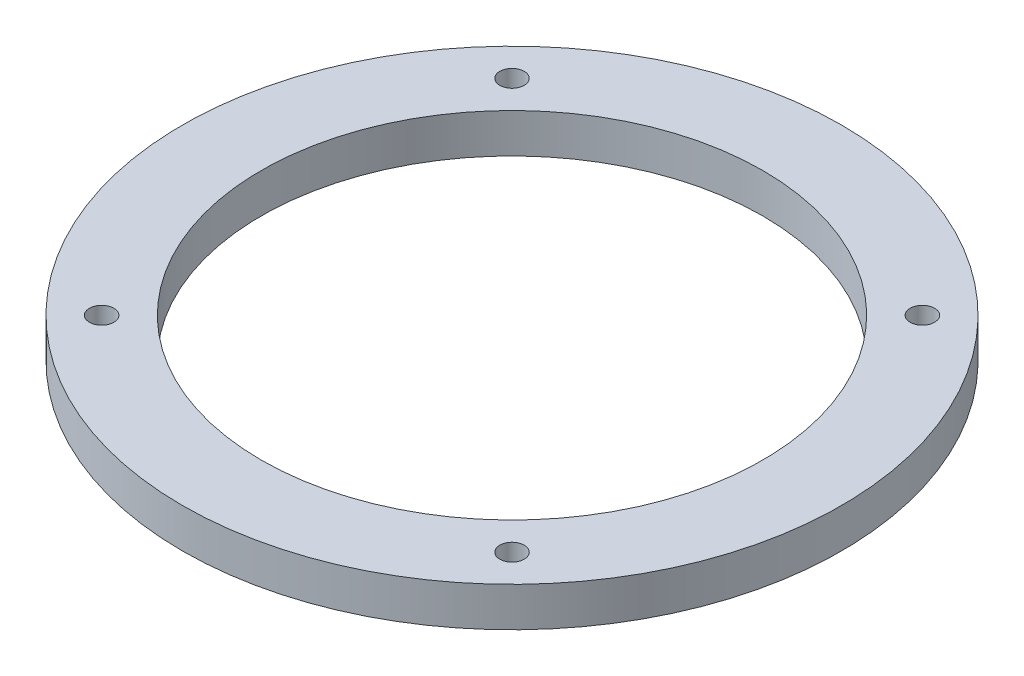
SolidWorks part; units mm, degrees
ref_plane "Alzado" through (0, 0, 0) normal (0, 0, 1) x (1, 0, 0)
ref_plane "Planta" through (0, 0, 0) normal (0, 1, 0) x (1, 0, 0)
ref_plane "Vista lateral" through (0, 0, 0) normal (1, 0, 0) x (0, 0, -1)
sketch "Croquis1" plane through (0, 0, 0) normal (0, 1, 0) x (1, 0, 0)
  line L1 (-26.05, -26.05) -> (26.05, -26.05) construction
  line L2 (-26.05, -26.05) -> (-26.05, 26.05) construction
  line L3 (-26.05, 26.05) -> (26.05, 26.05) construction
  line L4 (26.05, -26.05) -> (26.05, 26.05) construction
  line L5 (-26.05, -26.05) -> (26.05, 26.05) construction
  line L6 (-26.05, 26.05) -> (26.05, -26.05) construction
  circle A7 centre (-26.05, 26.05) radius 1.55
  circle A8 centre (0, 0) radius 36.8403 construction
  circle A9 centre (0, 0) radius 41.8403
  circle A10 centre (0, 0) radius 31.8403
  circle A11 centre (26.05, 26.05) radius 1.55
  circle A12 centre (26.05, -26.05) radius 1.55
  circle A13 centre (-26.05, -26.05) radius 1.55
  point P18 (0, 0)
  point P23 (0, 0)
  dimension "D1" = 52.1
  dimension "D2" = 3.1
  dimension "D3" = 5
  dimension "D4" = 5
  dimension "D5" = 4
extrude "Saliente-Extruir1" add sketch "Croquis1" along normal blind 5
